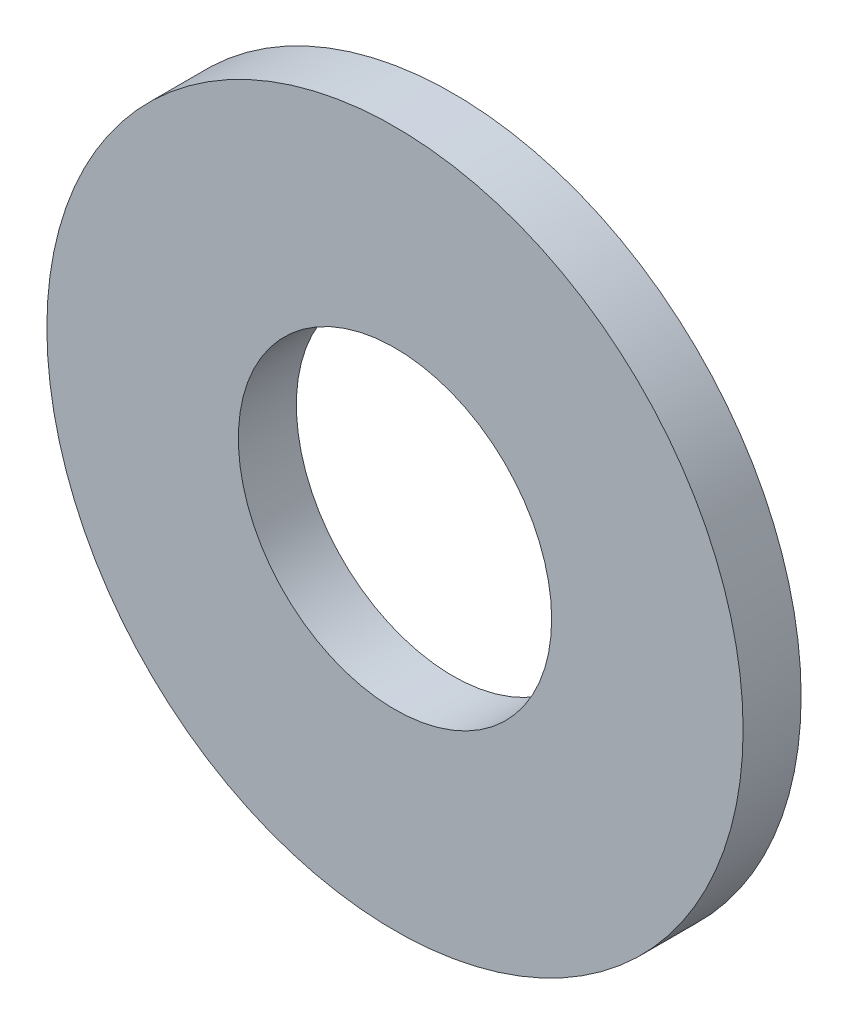
SolidWorks part; units mm, degrees
material "AISI Тип A2 Инструментальная сталь"
ref_plane "Front" through (0, 0, 0) normal (0, 0, 1) x (1, 0, 0)
ref_plane "Top" through (0, 0, 0) normal (0, 1, 0) x (1, 0, 0)
ref_plane "Right" through (0, 0, 0) normal (1, 0, 0) x (0, 0, -1)
sketch "Эскиз1" plane through (0, 0, 0) normal (0, 0, 1) x (1, 0, 0)
  circle A0 centre (0, 0) radius 3
  circle A1 centre (0, 0) radius 1.35
  dimension "D1" = 6
  dimension "D2" = 2.7
extrude "Бобышка-Вытянуть1" add sketch "Эскиз1" along normal blind 0.5
